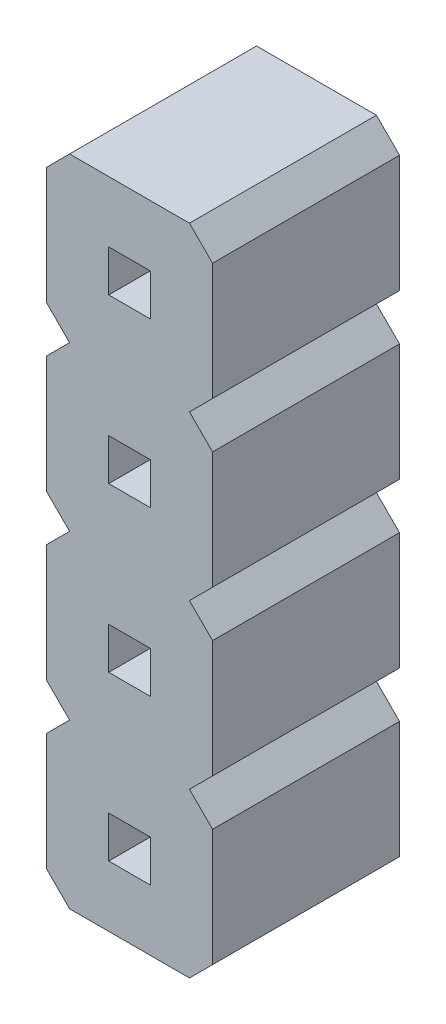
SolidWorks part; units mm, degrees
ref_plane "Alzado" through (0, 0, 0) normal (0, 0, 1) x (1, 0, 0)
ref_plane "Planta" through (0, 0, 0) normal (0, 1, 0) x (1, 0, 0)
ref_plane "Vista lateral" through (0, 0, 0) normal (1, 0, 0) x (0, 0, -1)
sketch "pin_drawing" plane through (0, 0, 0) normal (0, 0, 1) x (1, 0, 0)
  line L0 (0.9525, -0.932) -> (0, -0.932) construction
  line L1 (0, 2.1464) -> (0, 0.3536)
  line L2 (0, -0.3536) -> (0, -2.1464)
  line L3 (0, -0.3536) -> (0.3536, 0)
  line L4 (1.5885, -1.568) -> (2.541, -1.568) construction
  line L5 (0, 2.1464) -> (0.3536, 2.5)
  line L6 (2.541, -0.3536) -> (2.541, -2.1464)
  line L7 (0.9525, -1.25) -> (0.9525, -0.932) construction
  line L8 (2.541, -2.1464) -> (2.1874, -2.5)
  line L9 (2.1874, 0) -> (2.541, -0.3536)
  line L10 (1.5885, -1.25) -> (1.5885, -1.568) construction
  line L11 (0.3536, -2.5) -> (0, -2.1464)
  line L12 (0.9525, -0.932) -> (1.5885, -0.932)
  line L13 (0.9525, -0.932) -> (0.9525, -1.568)
  line L14 (0.9525, -1.568) -> (1.5885, -1.568)
  line L15 (1.5885, -0.932) -> (1.5885, -1.568)
  line L16 (2.541, 2.1464) -> (2.541, 0.3536)
  line L17 (2.541, 0.3536) -> (2.1874, 0)
  line L18 (2.1874, 2.5) -> (2.541, 2.1464)
  line L19 (0.3536, 0) -> (0, 0.3536)
  line L20 (0.9525, 1.568) -> (1.5885, 1.568)
  line L21 (0.9525, 1.568) -> (0.9525, 0.932)
  line L22 (0.9525, 0.932) -> (1.5885, 0.932)
  line L23 (1.5885, 1.568) -> (1.5885, 0.932)
  line L24 (0.9525, 1.568) -> (0, 1.568) construction
  line L25 (1.5885, 0.932) -> (2.541, 0.932) construction
  line L26 (0.9525, 1.25) -> (0.9525, 1.568) construction
  line L27 (1.5885, 1.25) -> (1.5885, 0.932) construction
  line L28 (0, 4.6464) -> (0, 2.8536)
  line L29 (0, 4.6464) -> (0.3536, 5)
  line L30 (2.541, 4.6464) -> (2.541, 2.8536)
  line L31 (2.541, 2.8536) -> (2.1874, 2.5)
  line L32 (2.1874, 5) -> (2.541, 4.6464)
  line L33 (0.3536, 2.5) -> (0, 2.8536)
  line L34 (0.9525, 4.068) -> (1.5885, 4.068)
  line L35 (0.9525, 4.068) -> (0.9525, 3.432)
  line L36 (0.9525, 3.432) -> (1.5885, 3.432)
  line L37 (1.5885, 4.068) -> (1.5885, 3.432)
  line L38 (0.9525, 4.068) -> (0, 4.068) construction
  line L39 (1.5885, 3.432) -> (2.541, 3.432) construction
  line L40 (0.9525, 3.75) -> (0.9525, 4.068) construction
  line L41 (1.5885, 3.75) -> (1.5885, 3.432) construction
  line L42 (0, 7.1464) -> (0, 5.3536)
  line L43 (0, 7.1464) -> (0.3536, 7.5)
  line L44 (2.541, 7.1464) -> (2.541, 5.3536)
  line L45 (2.541, 5.3536) -> (2.1874, 5)
  line L46 (2.1874, 7.5) -> (2.541, 7.1464)
  line L47 (0.3536, 5) -> (0, 5.3536)
  line L48 (0.9525, 6.568) -> (1.5885, 6.568)
  line L49 (0.9525, 6.568) -> (0.9525, 5.932)
  line L50 (0.9525, 5.932) -> (1.5885, 5.932)
  line L51 (1.5885, 6.568) -> (1.5885, 5.932)
  line L52 (0.9525, 6.568) -> (0, 6.568) construction
  line L53 (1.5885, 5.932) -> (2.541, 5.932) construction
  line L54 (0.9525, 6.25) -> (0.9525, 6.568) construction
  line L55 (1.5885, 6.25) -> (1.5885, 5.932) construction
  line L56 (0, 9.6464) -> (0, 7.8536) construction
  line L57 (0, 9.6464) -> (0.3536, 10) construction
  line L58 (2.541, 9.6464) -> (2.541, 7.8536) construction
  line L59 (2.541, 7.8536) -> (2.1874, 7.5) construction
  line L60 (2.1874, 10) -> (2.541, 9.6464) construction
  line L61 (0.3536, 7.5) -> (0, 7.8536) construction
  line L62 (0.9525, 9.068) -> (1.5885, 9.068) construction
  line L63 (0.9525, 9.068) -> (0.9525, 8.432) construction
  line L64 (0.9525, 8.432) -> (1.5885, 8.432) construction
  line L65 (1.5885, 9.068) -> (1.5885, 8.432) construction
  line L66 (0.9525, 9.068) -> (0, 9.068) construction
  line L67 (1.5885, 8.432) -> (2.541, 8.432) construction
  line L68 (0.9525, 8.75) -> (0.9525, 9.068) construction
  line L69 (1.5885, 8.75) -> (1.5885, 8.432) construction
  line L70 (0, 12.1464) -> (0, 10.3536) construction
  line L71 (0, 12.1464) -> (0.3536, 12.5) construction
  line L72 (2.541, 12.1464) -> (2.541, 10.3536) construction
  line L73 (2.541, 10.3536) -> (2.1874, 10) construction
  line L74 (2.1874, 12.5) -> (2.541, 12.1464) construction
  line L75 (0.3536, 10) -> (0, 10.3536) construction
  line L76 (0.9525, 11.568) -> (1.5885, 11.568) construction
  line L77 (0.9525, 11.568) -> (0.9525, 10.932) construction
  line L78 (0.9525, 10.932) -> (1.5885, 10.932) construction
  line L79 (1.5885, 11.568) -> (1.5885, 10.932) construction
  line L80 (0.9525, 11.568) -> (0, 11.568) construction
  line L81 (1.5885, 10.932) -> (2.541, 10.932) construction
  line L82 (0.9525, 11.25) -> (0.9525, 11.568) construction
  line L83 (1.5885, 11.25) -> (1.5885, 10.932) construction
  line L84 (0, 14.6464) -> (0, 12.8536) construction
  line L85 (0, 14.6464) -> (0.3536, 15) construction
  line L86 (2.541, 14.6464) -> (2.541, 12.8536) construction
  line L87 (2.541, 12.8536) -> (2.1874, 12.5) construction
  line L88 (2.1874, 15) -> (2.541, 14.6464) construction
  line L89 (0.3536, 12.5) -> (0, 12.8536) construction
  line L90 (0.9525, 14.068) -> (1.5885, 14.068) construction
  line L91 (0.9525, 14.068) -> (0.9525, 13.432) construction
  line L92 (0.9525, 13.432) -> (1.5885, 13.432) construction
  line L93 (1.5885, 14.068) -> (1.5885, 13.432) construction
  line L94 (0.9525, 14.068) -> (0, 14.068) construction
  line L95 (1.5885, 13.432) -> (2.541, 13.432) construction
  line L96 (0.9525, 13.75) -> (0.9525, 14.068) construction
  line L97 (1.5885, 13.75) -> (1.5885, 13.432) construction
  line L98 (0, 17.1464) -> (0, 15.3536) construction
  line L99 (0, 17.1464) -> (0.3536, 17.5) construction
  line L100 (2.541, 17.1464) -> (2.541, 15.3536) construction
  line L101 (2.541, 15.3536) -> (2.1874, 15) construction
  line L102 (2.1874, 17.5) -> (2.541, 17.1464) construction
  line L103 (0.3536, 15) -> (0, 15.3536) construction
  line L104 (0.9525, 16.568) -> (1.5885, 16.568) construction
  line L105 (0.9525, 16.568) -> (0.9525, 15.932) construction
  line L106 (0.9525, 15.932) -> (1.5885, 15.932) construction
  line L107 (1.5885, 16.568) -> (1.5885, 15.932) construction
  line L108 (0.9525, 16.568) -> (0, 16.568) construction
  line L109 (1.5885, 15.932) -> (2.541, 15.932) construction
  line L110 (0.9525, 16.25) -> (0.9525, 16.568) construction
  line L111 (1.5885, 16.25) -> (1.5885, 15.932) construction
  line L112 (0, 19.6464) -> (0, 17.8536) construction
  line L113 (0, 19.6464) -> (0.3536, 20) construction
  line L114 (2.541, 19.6464) -> (2.541, 17.8536) construction
  line L115 (2.541, 17.8536) -> (2.1874, 17.5) construction
  line L116 (2.1874, 20) -> (2.541, 19.6464) construction
  line L117 (0.3536, 17.5) -> (0, 17.8536) construction
  line L118 (0.9525, 19.068) -> (1.5885, 19.068) construction
  line L119 (0.9525, 19.068) -> (0.9525, 18.432) construction
  line L120 (0.9525, 18.432) -> (1.5885, 18.432) construction
  line L121 (1.5885, 19.068) -> (1.5885, 18.432) construction
  line L122 (0.9525, 19.068) -> (0, 19.068) construction
  line L123 (1.5885, 18.432) -> (2.541, 18.432) construction
  line L124 (0.9525, 18.75) -> (0.9525, 19.068) construction
  line L125 (1.5885, 18.75) -> (1.5885, 18.432) construction
  line L126 (0, 22.1464) -> (0, 20.3536) construction
  line L127 (0, 22.1464) -> (0.3536, 22.5) construction
  line L128 (2.541, 22.1464) -> (2.541, 20.3536) construction
  line L129 (2.541, 20.3536) -> (2.1874, 20) construction
  line L130 (2.1874, 22.5) -> (2.541, 22.1464) construction
  line L131 (0.3536, 20) -> (0, 20.3536) construction
  line L132 (0.9525, 21.568) -> (1.5885, 21.568) construction
  line L133 (0.9525, 21.568) -> (0.9525, 20.932) construction
  line L134 (0.9525, 20.932) -> (1.5885, 20.932) construction
  line L135 (1.5885, 21.568) -> (1.5885, 20.932) construction
  line L136 (0.9525, 21.568) -> (0, 21.568) construction
  line L137 (1.5885, 20.932) -> (2.541, 20.932) construction
  line L138 (0.9525, 21.25) -> (0.9525, 21.568) construction
  line L139 (1.5885, 21.25) -> (1.5885, 20.932) construction
  line L140 (0, 24.6464) -> (0, 22.8536) construction
  line L141 (0, 24.6464) -> (0.3536, 25) construction
  line L142 (2.541, 24.6464) -> (2.541, 22.8536) construction
  line L143 (2.541, 22.8536) -> (2.1874, 22.5) construction
  line L144 (2.1874, 25) -> (2.541, 24.6464) construction
  line L145 (0.3536, 22.5) -> (0, 22.8536) construction
  line L146 (0.9525, 24.068) -> (1.5885, 24.068) construction
  line L147 (0.9525, 24.068) -> (0.9525, 23.432) construction
  line L148 (0.9525, 23.432) -> (1.5885, 23.432) construction
  line L149 (1.5885, 24.068) -> (1.5885, 23.432) construction
  line L150 (0.9525, 24.068) -> (0, 24.068) construction
  line L151 (1.5885, 23.432) -> (2.541, 23.432) construction
  line L152 (0.9525, 23.75) -> (0.9525, 24.068) construction
  line L153 (1.5885, 23.75) -> (1.5885, 23.432) construction
  line L154 (0, 27.1464) -> (0, 25.3536) construction
  line L155 (0, 27.1464) -> (0.3536, 27.5) construction
  line L156 (2.541, 27.1464) -> (2.541, 25.3536) construction
  line L157 (2.541, 25.3536) -> (2.1874, 25) construction
  line L158 (2.1874, 27.5) -> (2.541, 27.1464) construction
  line L159 (0.3536, 25) -> (0, 25.3536) construction
  line L160 (0.9525, 26.568) -> (1.5885, 26.568) construction
  line L161 (0.9525, 26.568) -> (0.9525, 25.932) construction
  line L162 (0.9525, 25.932) -> (1.5885, 25.932) construction
  line L163 (1.5885, 26.568) -> (1.5885, 25.932) construction
  line L164 (0.9525, 26.568) -> (0, 26.568) construction
  line L165 (1.5885, 25.932) -> (2.541, 25.932) construction
  line L166 (0.9525, 26.25) -> (0.9525, 26.568) construction
  line L167 (1.5885, 26.25) -> (1.5885, 25.932) construction
  line L168 (2.1874, -2.5) -> (0.3536, -2.5)
  line L169 (0.3536, 27.5) -> (2.1874, 27.5) construction
  line L170 (0.3536, 7.5) -> (2.1874, 7.5)
  dimension "D1" = 0.318
  dimension "D2" = 0.9525
  dimension "D3" = 0.5
  dimension "D4" = 135
  dimension "D5" = 0.5
  dimension "D6" = 135
  dimension "D7" = 12
extrude "Boss-Extrude1" add sketch "pin_drawing" along normal blind 2.86
